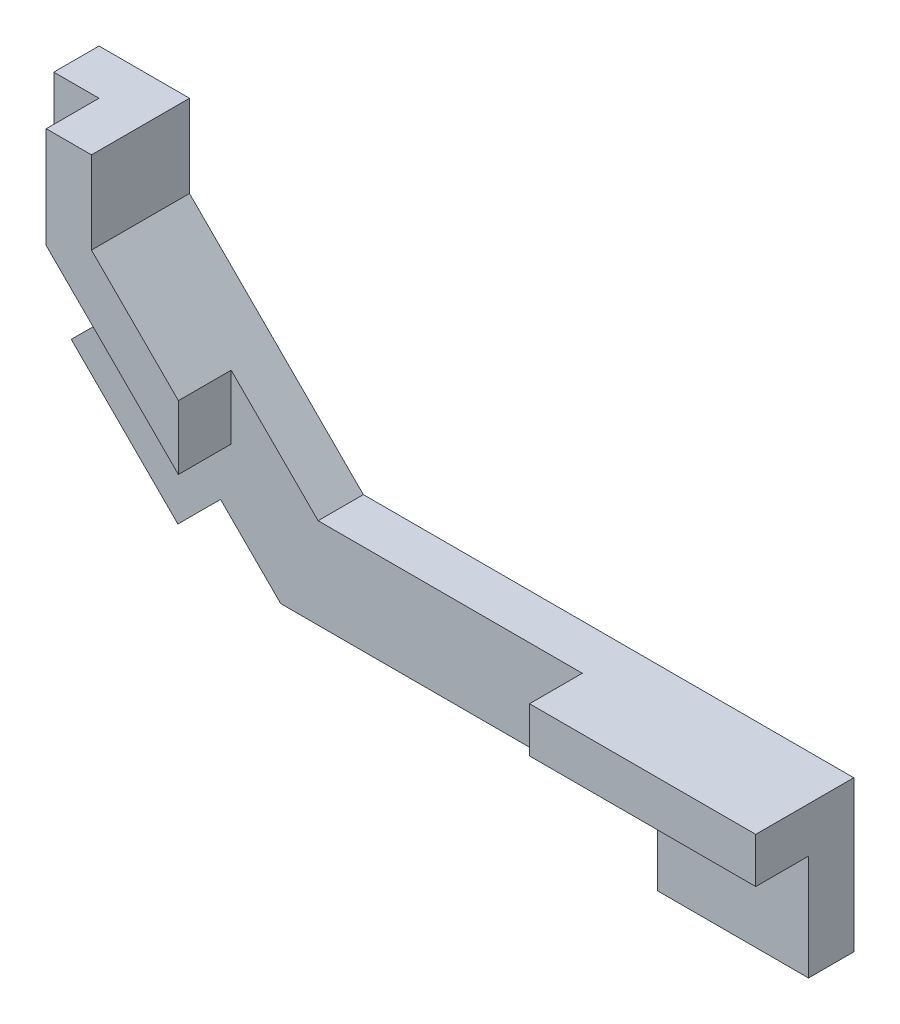
SolidWorks part; units mm, degrees
ref_plane "Front Plane" through (0, 0, 0) normal (0, 0, 1) x (1, 0, 0)
ref_plane "Top Plane" through (0, 0, 0) normal (0, 1, 0) x (1, 0, 0)
ref_plane "Right Plane" through (0, 0, 0) normal (1, 0, 0) x (0, 0, -1)
sketch "Sketch1" plane through (0, 0, 0) normal (0, 1, 0) x (1, 0, 0)
  line L1 (17.5, -1.5) -> (-17.5, -1.5)
  line L2 (17.5, -1.5) -> (17.5, 1.5)
  line L3 (17.5, 1.5) -> (-17.5, 1.5)
  line L4 (-17.5, -1.5) -> (-17.5, 1.5)
  line L5 (17.5, -1.5) -> (-17.5, 1.5) construction
  line L6 (17.5, 1.5) -> (-17.5, -1.5) construction
  point P0 (0, 0)
  dimension "D1" = 3
  dimension "D2" = 35
extrude "Boss-Extrude1" add sketch "Sketch1" along normal blind 6
sketch "Sketch2" plane through (0, 0, 1.5) normal (0, 0, 1) x (1, 0, 0)
  line L0 (-17.5, 0) -> (-32.5472, 15.0472)
  line L1 (-32.5472, 15.0472) -> (-32.5472, 22.9972)
  line L2 (-32.5472, 22.9972) -> (-26.5472, 22.9972)
  line L3 (-26.5472, 22.9972) -> (-26.5472, 17.5272)
  line L4 (-26.5472, 17.5272) -> (-15.02, 6)
  line L5 (-17.5, 6) -> (17.5, 6) construction
  line L6 (-17.5, 0) -> (17.5, 0) construction
  line L7 (-17.5, 0) -> (-17.5, 6)
  line L8 (-17.5, 6) -> (-15.02, 6)
  dimension "D1" = 6
  dimension "D2" = 21.28
  dimension "D3" = 7.95
  dimension "D4" = 135
  dimension "D5" = 5.47
extrude "Boss-Extrude2" add sketch "Sketch2" against normal up to surface (3 mm away) up to face at (0, 3, -1.5)
sketch "Sketch3" plane through (0, 0, 1.5) normal (0, 0, 1) x (1, 0, 0)
  line L0 (-29.5472, 22.9972) -> (-26.5472, 22.9972)
  line L1 (-26.5472, 22.9972) -> (-32.5472, 22.9972) construction
  line L2 (-26.5472, 22.9972) -> (-26.5472, 17.5272)
  line L3 (-26.5472, 17.5272) -> (-20.7836, 11.7636)
  line L4 (2.5, 6) -> (17.5, 6)
  line L5 (17.5, 6) -> (17.5, 3)
  line L6 (17.5, 6) -> (17.5, 0) construction
  line L7 (17.5, 3) -> (2.5, 3)
  line L8 (-20.7836, 7.521) -> (-29.5472, 16.2846)
  line L9 (-29.5472, 16.2846) -> (-29.5472, 22.9972)
  line L10 (2.5, 6) -> (2.5, 3)
  line L11 (-20.7836, 11.7636) -> (-20.7836, 7.521)
  line M11 (17.5, 0) -> (17.5, 6)
  line M12 (17.5, 6) -> (-15.02, 6)
  line M13 (-15.02, 6) -> (-26.5472, 17.5272)
  line M14 (-26.5472, 17.5272) -> (-26.5472, 22.9972)
  line M15 (-26.5472, 22.9972) -> (-32.5472, 22.9972)
  dimension "D1" = 3
  dimension "D2" = 15
  dimension "D3" = 5.7636
  dimension "D4" = 4.2426
extrude "Boss-Extrude3" add sketch "Sketch3" along normal blind 3.5 and the other way up to surface (3 mm away) contours L11 L9 L8 M13 M14 M15 | L10 L7 M12 M11
sketch "Sketch4" plane through (0, 0, 0) normal (0, -1, 0) x (1, 0, 0)
  line L1 (7.5, -1.5) -> (17.5, -1.5)
  line L2 (7.5, -1.5) -> (7.5, 1.5)
  line L3 (7.5, 1.5) -> (17.5, 1.5)
  line L4 (17.5, -1.5) -> (17.5, 1.5)
  line L5 (7.5, -1.5) -> (17.5, 1.5) construction
  line L6 (7.5, 1.5) -> (17.5, -1.5) construction
  point P0 (12.5, 0)
  dimension "D1" = 10
extrude "Boss-Extrude4" add sketch "Sketch4" along normal blind 4
sketch "Sketch5" plane through (-8.75, -8.75, 0) normal (-0.7071, -0.7071, 0) x (0, 0, 1)
  line L0 (-1.5, 23.0144) -> (1.5, 23.0144) construction
  line L1 (-1.5, 12.3744) -> (-1.5, 33.6544) construction
  line L2 (1.5, 33.6544) -> (1.5, 12.3744) construction
  line L4 (1.5, 18.0144) -> (-1.5, 18.0144)
  line L5 (1.5, 18.0144) -> (1.5, 28.0144)
  line L6 (1.5, 28.0144) -> (-1.5, 28.0144)
  line L7 (-1.5, 18.0144) -> (-1.5, 28.0144)
  line L8 (1.5, 18.0144) -> (-1.5, 28.0144) construction
  line L9 (1.5, 28.0144) -> (-1.5, 18.0144) construction
  point P6 (0, 23.0144)
  dimension "D1" = 10
extrude "Boss-Extrude5" add sketch "Sketch5" along normal blind 4
